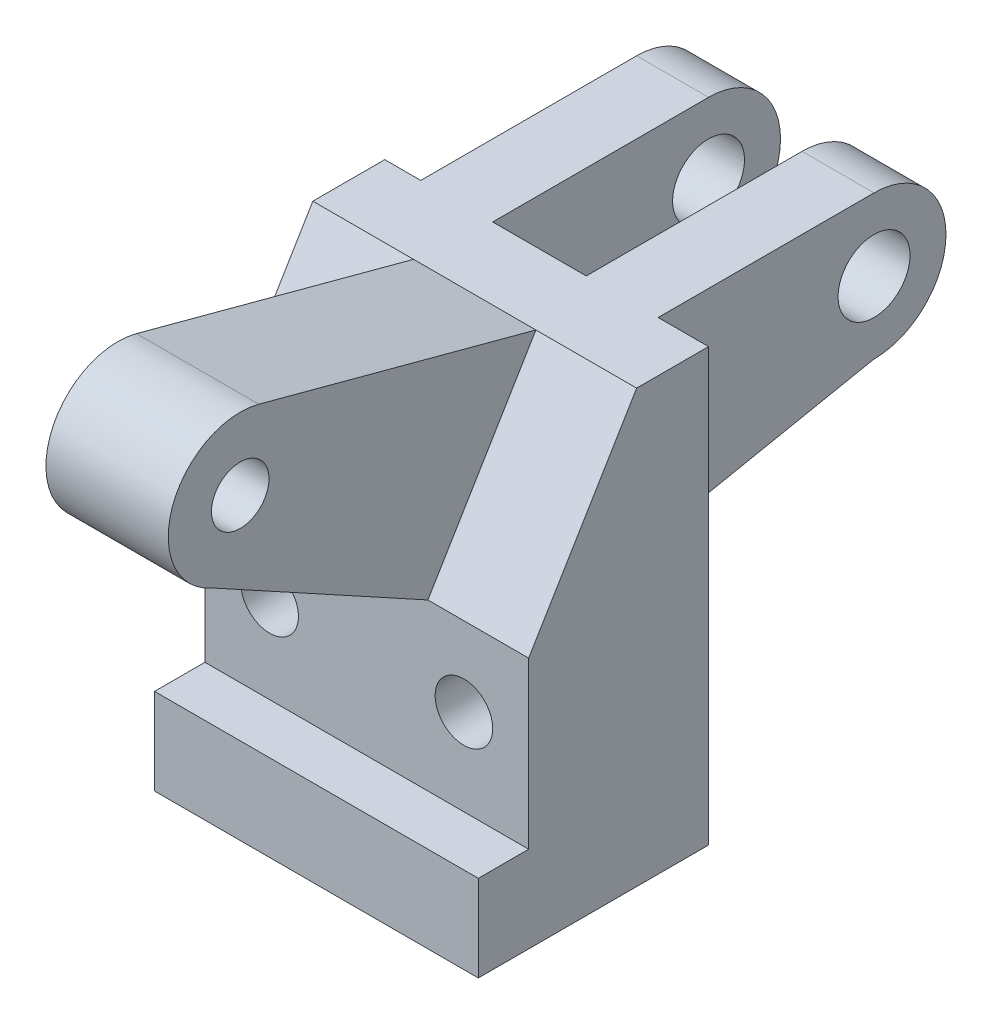
SolidWorks part; units mm, degrees
ref_plane "Front Plane" through (0, 0, 0) normal (0, 0, 1) x (1, 0, 0)
ref_plane "Top Plane" through (0, 0, 0) normal (0, 1, 0) x (1, 0, 0)
ref_plane "Right Plane" through (0, 0, 0) normal (1, 0, 0) x (0, 0, -1)
sketch "Sketch1" plane through (0, 0, 0) normal (0, 1, 0) x (1, 0, 0)
  line L0 (0, 0) -> (1143, 0)
  line L1 (1143, 0) -> (1143, -635)
  line L2 (1143, -635) -> (0, -635)
  line L3 (0, -635) -> (0, 0)
  dimension "D1" = 1143
  dimension "D2" = 635
extrude "Boss-Extrude1" add sketch "Sketch1" along normal blind 584.2
sketch "Sketch2" plane through (0, 0, 0) normal (0, -1, 0) x (1, 0, 0)
  line L0 (1143, 635) -> (1143, 812.8)
  line L1 (1143, 812.8) -> (0, 812.8)
  line L2 (0, 812.8) -> (0, 635)
  line L3 (0, 635) -> (1143, 635)
  dimension "D1" = 177.8
extrude "Boss-Extrude2" add sketch "Sketch2" against normal blind 304.8
sketch "Sketch4" plane through (0, 584.2, 0) normal (0, 1, 0) x (1, 0, 0)
  line L0 (0, 0) -> (1143, 0)
  line L1 (1143, 0) -> (1143, -635)
  line L2 (1143, -635) -> (0, -635)
  line L3 (0, -635) -> (0, 0)
extrude "Boss-Extrude3" add sketch "Sketch4" along normal blind 304.8
sketch "Sketch5" plane through (0, 0, 0) normal (-1, 0, 0) x (0, 0, 1)
  line L0 (0, 0) -> (0, 1524)
  line L1 (0, 1524) -> (254, 1524)
  line L2 (254, 1524) -> (254, 0)
  line L3 (0, 0) -> (812.8, 0) construction
  line L4 (254, 0) -> (0, 0)
  dimension "D1" = 1524
  dimension "D2" = 254
extrude "Boss-Extrude4" add sketch "Sketch5" against normal blind 1143
sketch "Sketch6" plane through (0, 0, 0) normal (-1, 0, 0) x (0, 0, 1)
  line L0 (254, 1524) -> (635, 889)
  line L1 (635, 889) -> (254, 889)
  line L2 (254, 889) -> (254, 1524)
extrude "Boss-Extrude5" add sketch "Sketch6" against normal blind 1143
sketch "Sketch8" plane through (0, 1524, 0) normal (0, 1, 0) x (1, 0, 0)
  line L0 (0, 0) -> (127, 0)
  line L1 (1143, 0) -> (0, 0) construction
  line L2 (127, 0) -> (127, 762)
  line L3 (127, 762) -> (381, 762)
  line L4 (381, 762) -> (381, 0)
  line L5 (381, 0) -> (127, 0)
  line M7 (1143, 0) -> (0, 0)
  dimension "D1" = 254
  dimension "5" = 127
  dimension "D2" = 762
extrude "Boss-Extrude6" add sketch "Sketch8" against normal blind 660.4 contours L4 L3 L2 M7
sketch "Sketch9" plane through (127, 0, 0) normal (-1, 0, 0) x (0, 0, 1)
  line L1 (-762, 1524) -> (-762, 1270)
  line L2 (-762, 863.6) -> (-762, 1524) construction
  line L3 (-762, 1016) -> (0, 863.6)
  line L4 (0, 863.6) -> (-762, 863.6)
  line L5 (-762, 863.6) -> (-762, 1016)
  circle A2 centre (-762, 1270) radius 254
  circle A3 centre (-762, 1270) radius 127
  line M3 (-762, 1524) -> (-762, 863.6)
  dimension "D1" = 254
extrude "Boss-Extrude7" add sketch "Sketch9" against normal blind 254 contours A3 A2 M3 | A3 A2 M3
sketch "Sketch10" plane through (127, 0, 0) normal (-1, 0, 0) x (0, 0, 1)
  circle A0 centre (-762, 1270) radius 127
extrude "Cut-Extrude2" cut sketch "Sketch10" against normal blind 254
sketch "Sketch11" plane through (127, 0, 0) normal (-1, 0, 0) x (0, 0, 1)
  line L0 (-762, 863.6) -> (0, 863.6)
  line L1 (0, 863.6) -> (-762, 1016)
  line L2 (-762, 1016) -> (-762, 863.6)
extrude "Cut-Extrude3" cut sketch "Sketch11" against normal blind 254
sketch "Sketch12" plane through (0, 1524, 0) normal (0, 1, 0) x (1, 0, 0)
  line L0 (381, 0) -> (711.2, 0)
  line L1 (1143, 0) -> (381, 0) construction
  line L2 (711.2, 0) -> (711.2, 762)
  line L3 (711.2, 762) -> (965.2, 762)
  line L4 (965.2, 762) -> (965.2, 0)
  line L5 (965.2, 0) -> (711.2, 0)
  line M7 (1143, 0) -> (381, 0)
  dimension "D1" = 330.2
  dimension "D2" = 762
  dimension "D3" = 254
extrude "Boss-Extrude8" add sketch "Sketch12" against normal blind 660.4 contours L4 L3 L2 M7
sketch "Sketch13" plane through (965.2, 0, 0) normal (1, 0, 0) x (0, 0, -1)
  circle A0 centre (762, 1270) radius 127
  circle A1 centre (762, 1270) radius 254
extrude "Boss-Extrude9" add sketch "Sketch13" against normal blind 254
sketch "Sketch14" plane through (965.2, 0, 0) normal (1, 0, 0) x (0, 0, -1)
  line L0 (762, 1143) -> (762, 1397) construction
  line L1 (762, 1016) -> (0, 863.6)
  line L2 (0, 863.6) -> (762, 863.6)
  line L3 (762, 863.6) -> (762, 1016)
  circle A0 centre (762, 1270) radius 127
extrude "Cut-Extrude4" cut sketch "Sketch14" against normal blind 254
sketch "Sketch15" plane through (0, 0, 635) normal (0, 0, 1) x (1, 0, 0)
  circle A0 centre (914.4, 609.6) radius 101.6
  circle A1 centre (228.6, 609.6) radius 101.6
extrude "Cut-Extrude5" cut sketch "Sketch15" against normal through all
ref_plane "Plane1" through (571.5, 0, 0) normal (1, 0, 0) x (0, 0, -1)
sketch "Sketch16" plane through (571.5, 0, 0) normal (1, 0, 0) x (0, 0, -1)
  line L0 (-635, 889) -> (-1397.9317, 1307.2382)
  line L2 (-254, 1524) -> (-635, 889)
  line L3 (-254, 1524) -> (-1232.0077, 1785.9886)
  arc A0 (-1232.0077, 1785.9886) -> (-1397.9317, 1307.2382) centre (-1297.7319, 1540.6391) ccw
  circle A1 centre (-1297.7319, 1540.6391) radius 101.6
extrude "Boss-Extrude10" add sketch "Sketch16" along normal blind 215.9 and the other way blind 215.9
